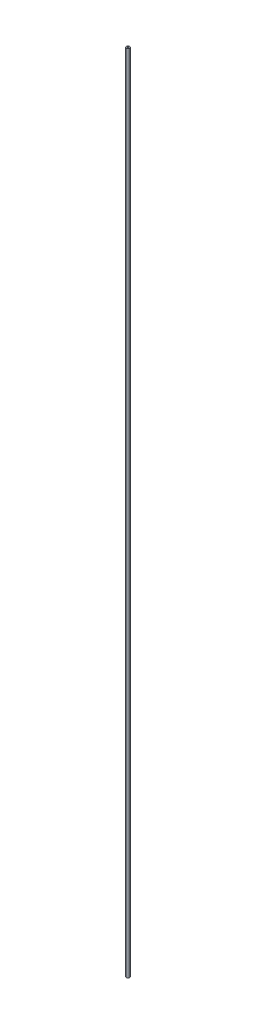
SolidWorks part; units mm, degrees
material "6061 Alloy"
ref_plane "Front Plane" through (0, 0, 0) normal (0, 0, 1) x (1, 0, 0)
ref_plane "Top Plane" through (0, 0, 0) normal (0, 1, 0) x (1, 0, 0)
ref_plane "Right Plane" through (0, 0, 0) normal (1, 0, 0) x (0, 0, -1)
sketch "Sketch1" plane through (0, 0, 0) normal (0, 1, 0) x (1, 0, 0)
  circle A0 centre (0, 0) radius 3.175
  circle A1 centre (0, 0) radius 1.524
  dimension "D1" = 6.35
  dimension "D2" = 3.048
extrude "Boss-Extrude1" add sketch "Sketch1" along normal mid plane 1524
